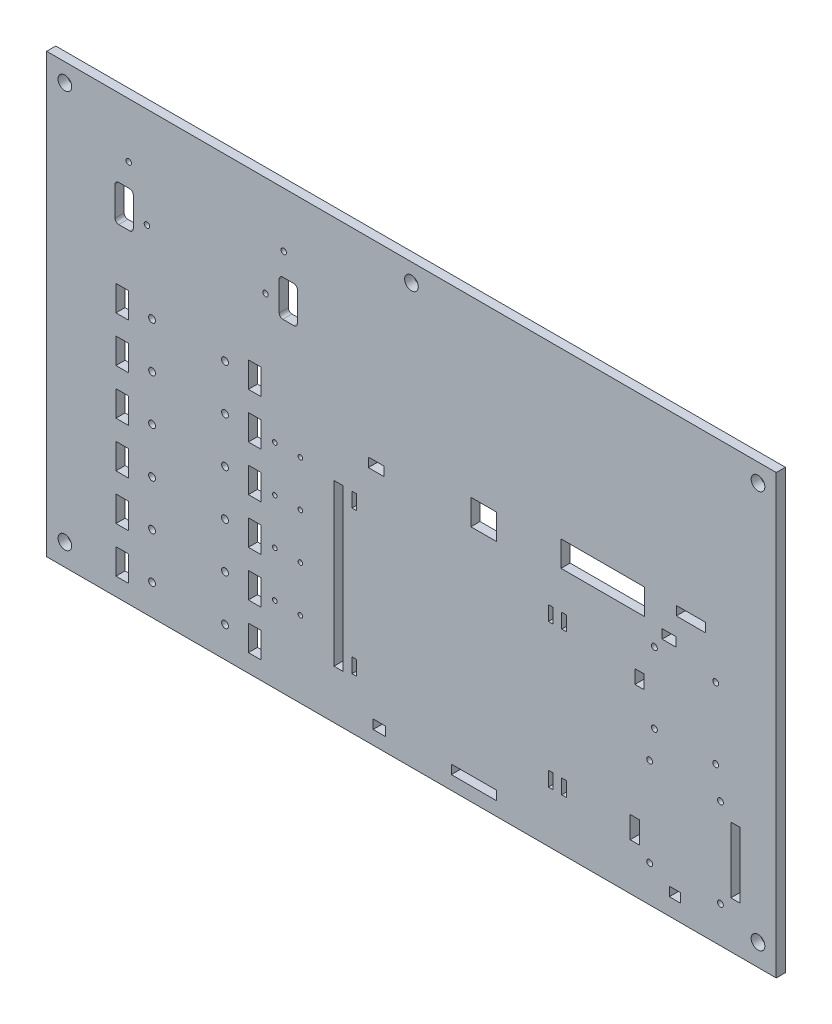
SolidWorks part; units mm, degrees
material "Acrylic (Medium-high impact)"
ref_plane "Front Plane" through (0, 0, 0) normal (0, 0, 1) x (1, 0, 0)
ref_plane "Top Plane" through (0, 0, 0) normal (0, 1, 0) x (1, 0, 0)
ref_plane "Right Plane" through (0, 0, 0) normal (1, 0, 0) x (0, 0, -1)
sketch "Sketch1" plane through (0, 0, 0) normal (0, 0, 1) x (1, 0, 0)
  line L1 (-249.2075, 101.7065) -> (258.7925, 101.7065)
  line L2 (-249.2075, 101.7065) -> (-249.2075, -203.0935)
  line L3 (-249.2075, -203.0935) -> (258.7925, -203.0935)
  line L4 (258.7925, 101.7065) -> (258.7925, -203.0935)
  dimension "D1" = 508
  dimension "D2" = 304.8
extrude "Boss-Extrude1" add sketch "Sketch1" along normal blind 6.35
sketch "Sketch2" plane through (0, 0, 6.35) normal (0, 0, 1) x (1, 0, 0)
  line L0 (-249.2075, 76.3065) -> (258.7925, 76.3065) construction
  line L1 (-223.8075, 76.3065) -> (-223.8075, -203.0935) construction
  line L2 (233.3925, 76.3065) -> (233.3925, -203.0935) construction
  line L3 (-185.7075, -181.7575) -> (-115.0955, -181.7575) construction
  line L4 (-249.2075, 101.7065) -> (-249.2075, -203.0935)
  line L5 (-249.2075, -203.0935) -> (258.7925, -203.0935)
  line L6 (258.7925, -203.0935) -> (258.7925, 101.7065)
  line L7 (258.7925, 101.7065) -> (-249.2075, 101.7065)
  line L8 (-249.2075, 101.7065) -> (-249.2075, -203.0935)
  line L9 (-249.2075, -203.0935) -> (258.7925, -203.0935)
  line L10 (258.7925, -203.0935) -> (258.7925, 101.7065)
  line L11 (258.7925, 101.7065) -> (-249.2075, 101.7065)
  line L12 (-185.7075, -166.7715) -> (-115.0955, -166.7715) construction
  line L13 (-185.7075, -166.7715) -> (-185.7075, -196.7435) construction
  line L14 (-185.7075, -196.7435) -> (-115.0955, -196.7435) construction
  line L15 (-115.0955, -166.7715) -> (-115.0955, -196.7435) construction
  line L16 (-150.4015, -166.7715) -> (-150.4015, -196.7435) construction
  line L17 (-185.7075, -135.0215) -> (-115.0955, -135.0215) construction
  line L18 (-185.7075, -135.0215) -> (-185.7075, -164.9935) construction
  line L19 (-185.7075, -164.9935) -> (-115.0955, -164.9935) construction
  line L20 (-115.0955, -135.0215) -> (-115.0955, -164.9935) construction
  line L21 (-185.7075, -150.0075) -> (-115.0955, -150.0075) construction
  line L22 (-150.4015, -135.0215) -> (-150.4015, -164.9935) construction
  line L23 (-185.7075, -103.2715) -> (-115.0955, -103.2715) construction
  line L24 (-185.7075, -103.2715) -> (-185.7075, -133.2435) construction
  line L25 (-185.7075, -133.2435) -> (-115.0955, -133.2435) construction
  line L26 (-115.0955, -103.2715) -> (-115.0955, -133.2435) construction
  line L27 (-185.7075, -118.2575) -> (-115.0955, -118.2575) construction
  line L28 (-150.4015, -103.2715) -> (-150.4015, -133.2435) construction
  line L29 (-185.7075, -71.5215) -> (-115.0955, -71.5215) construction
  line L30 (-185.7075, -71.5215) -> (-185.7075, -101.4935) construction
  line L31 (-185.7075, -101.4935) -> (-115.0955, -101.4935) construction
  line L32 (-115.0955, -71.5215) -> (-115.0955, -101.4935) construction
  line L33 (-200.9475, -181.7575) -> (-192.0575, -181.7575) construction
  line L34 (-192.0575, -190.6475) -> (-200.9475, -190.6475)
  line L35 (-192.0575, -190.6475) -> (-192.0575, -172.8675)
  line L36 (-192.0575, -172.8675) -> (-200.9475, -172.8675)
  line L37 (-185.7075, -86.5075) -> (-115.0955, -86.5075) construction
  line L38 (-150.4015, -71.5215) -> (-150.4015, -101.4935) construction
  line L39 (-185.7075, -39.7715) -> (-115.0955, -39.7715) construction
  line L40 (-185.7075, -39.7715) -> (-185.7075, -69.7435) construction
  line L41 (-185.7075, -69.7435) -> (-115.0955, -69.7435) construction
  line L42 (-115.0955, -39.7715) -> (-115.0955, -69.7435) construction
  line L43 (-185.7075, -54.7575) -> (-115.0955, -54.7575) construction
  line L44 (-150.4015, -39.7715) -> (-150.4015, -69.7435) construction
  line L45 (-185.7075, -8.0215) -> (-115.0955, -8.0215) construction
  line L46 (-185.7075, -8.0215) -> (-185.7075, -37.9935) construction
  line L47 (-185.7075, -37.9935) -> (-115.0955, -37.9935) construction
  line L48 (-115.0955, -8.0215) -> (-115.0955, -37.9935) construction
  line L49 (-185.7075, -23.0075) -> (-115.0955, -23.0075) construction
  line L50 (-150.4015, -8.0215) -> (-150.4015, -37.9935) construction
  line L51 (-200.9475, -190.6475) -> (-200.9475, -172.8675)
  line L52 (-200.9475, -158.8975) -> (-200.9475, -141.1175)
  line L53 (-192.0575, -158.8975) -> (-192.0575, -141.1175)
  line L54 (-192.0575, -141.1175) -> (-200.9475, -141.1175)
  line L55 (-192.0575, -158.8975) -> (-200.9475, -158.8975)
  line L56 (-200.9475, -127.1475) -> (-200.9475, -109.3675)
  line L57 (-192.0575, -127.1475) -> (-192.0575, -109.3675)
  line L58 (-192.0575, -109.3675) -> (-200.9475, -109.3675)
  line L59 (-192.0575, -127.1475) -> (-200.9475, -127.1475)
  line L60 (-200.9475, -95.3975) -> (-200.9475, -77.6175)
  line L61 (-192.0575, -95.3975) -> (-192.0575, -77.6175)
  line L62 (-192.0575, -77.6175) -> (-200.9475, -77.6175)
  line L63 (-192.0575, -95.3975) -> (-200.9475, -95.3975)
  line L64 (-200.9475, -63.6475) -> (-200.9475, -45.8675)
  line L65 (-192.0575, -63.6475) -> (-192.0575, -45.8675)
  line L66 (-192.0575, -45.8675) -> (-200.9475, -45.8675)
  line L67 (-192.0575, -63.6475) -> (-200.9475, -63.6475)
  line L68 (-200.9475, -31.8975) -> (-200.9475, -14.1175)
  line L69 (-192.0575, -31.8975) -> (-192.0575, -14.1175)
  line L70 (-192.0575, -14.1175) -> (-200.9475, -14.1175)
  line L71 (-192.0575, -31.8975) -> (-200.9475, -31.8975)
  line L72 (-108.7455, -190.6475) -> (-99.8555, -190.6475)
  line L73 (-99.8555, -190.6475) -> (-99.8555, -172.8675)
  line L74 (-108.7455, -190.6475) -> (-108.7455, -172.8675)
  line L75 (-108.7455, -172.8675) -> (-99.8555, -172.8675)
  line L76 (-108.7455, -141.1175) -> (-99.8555, -141.1175)
  line L77 (-99.8555, -158.8975) -> (-99.8555, -141.1175)
  line L78 (-108.7455, -158.8975) -> (-108.7455, -141.1175)
  line L79 (-108.7455, -158.8975) -> (-99.8555, -158.8975)
  line L80 (-108.7455, -109.3675) -> (-99.8555, -109.3675)
  line L81 (-99.8555, -127.1475) -> (-99.8555, -109.3675)
  line L82 (-108.7455, -127.1475) -> (-108.7455, -109.3675)
  line L83 (-108.7455, -127.1475) -> (-99.8555, -127.1475)
  line L84 (-108.7455, -77.6175) -> (-99.8555, -77.6175)
  line L85 (-99.8555, -95.3975) -> (-99.8555, -77.6175)
  line L86 (-108.7455, -95.3975) -> (-108.7455, -77.6175)
  line L87 (-108.7455, -95.3975) -> (-99.8555, -95.3975)
  line L88 (-108.7455, -45.8675) -> (-99.8555, -45.8675)
  line L89 (-99.8555, -63.6475) -> (-99.8555, -45.8675)
  line L90 (-108.7455, -63.6475) -> (-108.7455, -45.8675)
  line L91 (-108.7455, -63.6475) -> (-99.8555, -63.6475)
  line L92 (-108.7455, -14.1175) -> (-99.8555, -14.1175)
  line L93 (220.6925, -70.5055) -> (169.8925, -70.5055) construction
  line L94 (-99.8555, -31.8975) -> (-99.8555, -14.1175)
  line L95 (220.6925, -41.8035) -> (220.6925, -99.2075) construction
  line L96 (-108.7455, -31.8975) -> (-108.7455, -14.1175)
  line L97 (220.6925, -41.8035) -> (169.8925, -41.8035) construction
  line L98 (-108.7455, -31.8975) -> (-99.8555, -31.8975)
  line L99 (169.8925, -41.8035) -> (169.8925, -99.2075) construction
  line L100 (220.6925, -99.2075) -> (169.8925, -99.2075) construction
  line L101 (166.7175, -65.743) -> (166.7175, -75.268)
  line L102 (166.7175, -65.743) -> (160.3675, -65.743)
  line L103 (160.3675, -65.743) -> (160.3675, -75.268)
  line L104 (166.7175, -75.268) -> (160.3675, -75.268)
  line L105 (166.7175, -70.5055) -> (160.3675, -70.5055) construction
  line L106 (195.2925, -41.8035) -> (195.2925, -99.2075) construction
  line L107 (179.354, -32.1515) -> (188.879, -32.1515)
  line L108 (179.354, -32.1515) -> (179.354, -38.5015)
  line L109 (179.354, -38.5015) -> (188.879, -38.5015)
  line L110 (188.879, -32.1515) -> (188.879, -38.5015)
  line L111 (184.1165, -32.1515) -> (184.1165, -38.5015) construction
  line L112 (-249.2075, 101.7065) -> (-249.2075, -203.0935) construction
  line L113 (-249.2075, -203.0935) -> (258.7925, -203.0935) construction
  line L114 (-39.6575, -40.4827) -> (106.3925, -40.4827) construction
  line L115 (-39.6575, -40.4827) -> (-39.6575, -184.0435) construction
  line L116 (-39.6575, -184.0435) -> (106.3925, -184.0435) construction
  line L117 (106.3925, -40.4827) -> (106.3925, -184.0435) construction
  line L118 (-21.8775, -187.2185) -> (-13.1399, -187.2185)
  line L119 (-21.8775, -187.2185) -> (-21.8775, -193.5685)
  line L120 (-21.8775, -193.5685) -> (-13.1399, -193.5685)
  line L121 (-13.1399, -187.2185) -> (-13.1399, -193.5685)
  line L122 (32.5801, -187.2185) -> (64.0761, -187.2185)
  line L123 (64.0761, -187.2185) -> (64.0761, -193.5685)
  line L124 (64.0761, -193.5685) -> (32.5801, -193.5685)
  line L125 (32.5801, -193.5685) -> (32.5801, -187.2185)
  line L126 (33.3675, -40.4827) -> (33.3675, -184.0435) construction
  line L127 (-42.8325, -169.0575) -> (-49.1825, -169.0575)
  line L128 (-42.8325, -169.0575) -> (-42.8325, -57.0435)
  line L129 (-42.8325, -57.0435) -> (-49.1825, -57.0435)
  line L130 (-49.1825, -169.0575) -> (-49.1825, -57.0435)
  line L131 (-14.2575, -30.9577) -> (-25.1795, -30.9577)
  line L132 (-14.2575, -30.9577) -> (-14.2575, -37.3077)
  line L133 (-14.2575, -37.3077) -> (-25.1795, -37.3077)
  line L134 (-25.1795, -30.9577) -> (-25.1795, -37.3077)
  line L135 (46.1945, -37.3077) -> (63.9745, -37.3077)
  line L136 (46.1945, -37.3077) -> (46.1945, -19.5277)
  line L137 (46.1945, -19.5277) -> (63.9745, -19.5277)
  line L138 (63.9745, -37.3077) -> (63.9745, -19.5277)
  line L139 (-39.6575, -112.2631) -> (106.3925, -112.2631) construction
  line L140 (-33.4345, -167.2795) -> (-33.4345, -157.1195)
  line L141 (-36.6095, -167.2795) -> (-36.6095, -157.1195)
  line L142 (-36.6095, -157.1195) -> (-33.4345, -157.1195)
  line L143 (-36.6095, -57.2467) -> (-33.4345, -57.2467)
  line L144 (-36.6095, -57.2467) -> (-36.6095, -67.4067)
  line L145 (-36.6095, -67.4067) -> (-33.4345, -67.4067)
  line L146 (-33.4345, -57.2467) -> (-33.4345, -67.4067)
  line L147 (-36.6095, -167.2795) -> (-33.4345, -167.2795)
  line L148 (103.3445, -167.2795) -> (103.3445, -157.1195)
  line L149 (100.1695, -167.2795) -> (100.1695, -157.1195)
  line L150 (103.3445, -157.1195) -> (100.1695, -157.1195)
  line L151 (103.3445, -167.2795) -> (100.1695, -167.2795)
  line L152 (103.3445, -67.4067) -> (100.1695, -67.4067)
  line L153 (100.1695, -57.2467) -> (100.1695, -67.4067)
  line L154 (103.3445, -57.2467) -> (103.3445, -67.4067)
  line L155 (103.3445, -57.2467) -> (100.1695, -57.2467)
  line L156 (109.4405, -167.2795) -> (109.4405, -157.1195)
  line L157 (112.6155, -167.2795) -> (112.6155, -157.1195)
  line L158 (109.4405, -167.2795) -> (112.6155, -167.2795)
  line L159 (109.4405, -157.1195) -> (112.6155, -157.1195)
  line L160 (109.4405, -67.4067) -> (112.6155, -67.4067)
  line L161 (109.4405, -57.2467) -> (109.4405, -67.4067)
  line L162 (112.6155, -57.2467) -> (112.6155, -67.4067)
  line L163 (109.4405, -57.2467) -> (112.6155, -57.2467)
  line L164 (86.0725, -10.0535) -> (275.667, -10.0535) construction
  line L165 (86.0725, -10.0535) -> (86.0725, 101.7065) construction
  line L166 (223.9945, -181.7575) -> (166.5905, -181.7575) construction
  line L167 (108.9325, -13.2285) -> (167.0985, -13.2285)
  line L168 (108.9325, -13.2285) -> (108.9325, -31.0085)
  line L169 (108.9325, -31.0085) -> (167.0985, -31.0085)
  line L170 (167.0985, -13.2285) -> (167.0985, -31.0085)
  line L171 (209.5165, -13.2285) -> (189.1965, -13.2285)
  line L172 (209.5165, -13.2285) -> (209.5165, -19.5785)
  line L173 (209.5165, -19.5785) -> (189.1965, -19.5785)
  line L174 (189.1965, -13.2285) -> (189.1965, -19.5785)
  line L175 (223.9945, -181.7575) -> (223.9945, -111.9075) construction
  line L176 (223.9945, -111.9075) -> (166.5905, -111.9075) construction
  line L177 (166.5905, -181.7575) -> (166.5905, -111.9075) construction
  line L178 (163.4155, -170.5815) -> (157.0655, -170.5815)
  line L179 (163.4155, -170.5815) -> (163.4155, -155.3415)
  line L180 (163.4155, -155.3415) -> (157.0655, -155.3415)
  line L181 (157.0655, -170.5815) -> (157.0655, -155.3415)
  line L182 (191.9905, -184.9325) -> (184.3705, -184.9325)
  line L183 (191.9905, -184.9325) -> (191.9905, -191.2825)
  line L184 (191.9905, -191.2825) -> (184.3705, -191.2825)
  line L185 (184.3705, -184.9325) -> (184.3705, -191.2825)
  line L186 (233.5195, -170.5815) -> (227.1695, -170.5815)
  line L187 (233.5195, -170.5815) -> (233.5195, -124.8615)
  line L188 (233.5195, -124.8615) -> (227.1695, -124.8615)
  line L189 (227.1695, -170.5815) -> (227.1695, -124.8615)
  line L190 (223.9945, -146.8325) -> (166.5905, -146.8325) construction
  line L191 (195.2925, -111.9075) -> (195.2925, -181.7575) construction
  line L192 (-188.8825, 24.8715) -> (-188.8825, 45.1915)
  line L193 (-74.5825, 22.3315) -> (-201.5825, 22.3315) construction
  line L194 (-74.5825, 22.3315) -> (-74.5825, 73.1315) construction
  line L195 (-74.5825, 73.1315) -> (-201.5825, 73.1315) construction
  line L196 (-201.5825, 22.3315) -> (-201.5825, 73.1315) construction
  line L197 (-191.4225, 47.7315) -> (-199.0425, 47.7315)
  line L198 (-201.5825, 45.1915) -> (-201.5825, 24.8715)
  line L199 (-199.0425, 22.3315) -> (-191.4225, 22.3315)
  line L200 (-138.0825, 73.1315) -> (-138.0825, 22.3315) construction
  line L201 (-84.7425, 47.7315) -> (-77.1225, 47.7315)
  line L202 (-74.5825, 45.1915) -> (-74.5825, 24.8715)
  line L203 (-77.1225, 22.3315) -> (-84.7425, 22.3315)
  line L204 (-87.2825, 24.8715) -> (-87.2825, 45.1915)
  circle A0 centre (-175.8015, -181.7575) radius 2.3812
  circle A1 centre (-125.0015, -181.7575) radius 2.3812
  circle A2 centre (-175.8015, -150.0075) radius 2.3812
  circle A3 centre (-125.0015, -150.0075) radius 2.3812
  circle A4 centre (-175.8015, -118.2575) radius 2.3812
  circle A5 centre (-125.0015, -118.2575) radius 2.3812
  circle A6 centre (-175.8015, -86.5075) radius 2.3812
  circle A7 centre (-125.0015, -86.5075) radius 2.3812
  circle A8 centre (-175.8015, -54.7575) radius 2.3812
  circle A9 centre (-125.0015, -54.7575) radius 2.3812
  circle A10 centre (-90.3305, -150.0075) radius 1.5875
  circle A11 centre (-72.5505, -150.0075) radius 1.5875
  circle A12 centre (-236.5075, -187.8535) radius 4.7625
  circle A13 centre (-236.5075, 89.0065) radius 4.7625
  circle A14 centre (4.7925, 89.0065) radius 4.7625
  circle A15 centre (246.0925, 89.0065) radius 4.7625
  circle A16 centre (246.0925, -187.8535) radius 4.7625
  circle A17 centre (-175.8015, -23.0075) radius 2.3812
  circle A18 centre (-125.0015, -23.0075) radius 2.3812
  circle A19 centre (-72.5505, -118.2575) radius 1.5875
  circle A20 centre (-90.3305, -118.2575) radius 1.5875
  circle A21 centre (-72.5505, -86.5075) radius 1.5875
  circle A22 centre (-90.3305, -86.5075) radius 1.5875
  circle A23 centre (-72.5505, -54.7575) radius 1.5875
  circle A24 centre (-90.3305, -54.7575) radius 1.5875
  circle A25 centre (216.6285, -45.8675) radius 2.032
  circle A26 centre (216.6285, -95.1435) radius 2.032
  circle A27 centre (173.9565, -95.1435) radius 2.032
  circle A28 centre (173.9565, -45.8675) radius 2.032
  circle A29 centre (219.9305, -177.6935) radius 2.032
  circle A30 centre (170.6545, -177.6935) radius 2.032
  circle A31 centre (170.6545, -115.9715) radius 2.032
  circle A32 centre (219.9305, -115.9715) radius 2.032
  circle A33 centre (-192.0575, 63.6065) radius 1.8987
  circle A34 centre (-84.1075, 63.6065) radius 1.8987
  circle A35 centre (-179.3575, 31.8565) radius 1.8987
  circle A36 centre (-96.8075, 31.8565) radius 1.8987
  arc A37 (-188.8825, 24.8715) -> (-191.4225, 22.3315) centre (-191.4225, 24.8715) cw
  arc A38 (-201.5825, 24.8715) -> (-199.0425, 22.3315) centre (-199.0425, 24.8715) ccw
  arc A39 (-199.0425, 47.7315) -> (-201.5825, 45.1915) centre (-199.0425, 45.1915) ccw
  arc A40 (-188.8825, 45.1915) -> (-191.4225, 47.7315) centre (-191.4225, 45.1915) ccw
  arc A41 (-77.1225, 47.7315) -> (-74.5825, 45.1915) centre (-77.1225, 45.1915) cw
  arc A42 (-74.5825, 24.8715) -> (-77.1225, 22.3315) centre (-77.1225, 24.8715) cw
  arc A43 (-87.2825, 24.8715) -> (-84.7425, 22.3315) centre (-84.7425, 24.8715) ccw
  arc A44 (-87.2825, 45.1915) -> (-84.7425, 47.7315) centre (-84.7425, 45.1915) cw
  point P298 (-188.8825, 22.3315)
  point P304 (-201.5825, 47.7315)
  dimension "D9" = 4.7625
  dimension "D13" = 9.525
  dimension "D27" = 17.78
  dimension "D26" = 3.175
  dimension "D36" = 4.064
  dimension "D48" = 4.064
  dimension "D100" = 4.064
  dimension "D106" = 4.064
  dimension "D109" = 3.7973
  dimension "D122" = 2.54
  dimension "D2" = 25.4
  dimension "D3" = 25.4
  dimension "D4" = 25.4
  dimension "D5" = 29.972
  dimension "D6" = 70.612
  dimension "D7" = 63.5
  dimension "D8" = 6.35
  dimension "D10" = 25.4
  dimension "D14" = 12.7
  dimension "D15" = 12.7
  dimension "D16" = 12.7
  dimension "D17" = 15.24
  dimension "D18" = 241.3
  dimension "D19" = 241.3
  dimension "D20" = 12.7
  dimension "D21" = 12.7
  dimension "D22" = 15.24
  dimension "D23" = 12.7
  dimension "D24" = 17.78
  dimension "D25" = 8.89
  dimension "D12" = 6.35
  dimension "D28" = 9.525
  dimension "D29" = 1.778
  dimension "D30" = 48.26
  dimension "D32" = 57.404
  dimension "D33" = 9.525
  dimension "D34" = 6.35
  dimension "D35" = 3.175
  dimension "D37" = 4.064
  dimension "D38" = 9.525
  dimension "D39" = 6.35
  dimension "D40" = 14.224
  dimension "D41" = 3.302
  dimension "D42" = 50.8
  dimension "D43" = 4.064
  dimension "D44" = 4.064
  dimension "D45" = 4.064
  dimension "D46" = 3.175
  dimension "D47" = 143.5608
  dimension "D49" = 6.35
  dimension "D50" = 146.05
  dimension "D51" = 17.78
  dimension "D52" = 8.7376
  dimension "D53" = 45.72
  dimension "D54" = 31.496
  dimension "D55" = 6.35
  dimension "D56" = 3.175
  dimension "D57" = 6.35
  dimension "D58" = 14.986
  dimension "D59" = 112.014
  dimension "D60" = 3.175
  dimension "D61" = 3.175
  dimension "D62" = 25.4
  dimension "D63" = 10.922
  dimension "D64" = 6.35
  dimension "D65" = 85.852
  dimension "D66" = 17.78
  dimension "D67" = 17.78
  dimension "D68" = 10.16
  dimension "D69" = 16.764
  dimension "D70" = 3.048
  dimension "D71" = 3.175
  dimension "D72" = 3.175
  dimension "D73" = 19.05
  dimension "D74" = 152.4
  dimension "D75" = 6.35
  dimension "D76" = 111.76
  dimension "D77" = 147.32
  dimension "D78" = 17.78
  dimension "D79" = 22.86
  dimension "D80" = 58.166
  dimension "D81" = 6.35
  dimension "D82" = 20.32
  dimension "D83" = 3.175
  dimension "D84" = 23.876
  dimension "D85" = 31.75
  dimension "D86" = 38.1
  dimension "D87" = 69.85
  dimension "D88" = 3.175
  dimension "D89" = 6.35
  dimension "D90" = 11.176
  dimension "D91" = 15.24
  dimension "D92" = 3.175
  dimension "D93" = 6.35
  dimension "D94" = 7.62
  dimension "D95" = 17.78
  dimension "D96" = 11.176
  dimension "D97" = 45.72
  dimension "D98" = 3.175
  dimension "D99" = 6.35
  dimension "D101" = 4.064
  dimension "D102" = 4.064
  dimension "D103" = 4.064
  dimension "D104" = 4.064
  dimension "D105" = 4.064
  dimension "D107" = 12.7
  dimension "D108" = 28.702
  dimension "D110" = 107.95
  dimension "D111" = 82.55
  dimension "D112" = 12.7
  dimension "D113" = 31.75
  dimension "D114" = 12.7
  dimension "D115" = 31.75
  dimension "D116" = 127
  dimension "D117" = 9.525
  dimension "D118" = 9.525
  dimension "D119" = 9.525
  dimension "D120" = 12.7
  dimension "D121" = 25.4
  dimension "D1" = 0
  dimension "D11" = 6
  dimension "D31" = 4
extrude "Cut-Extrude1" cut sketch "Sketch2" against normal blind 7.62 flip side to cut
